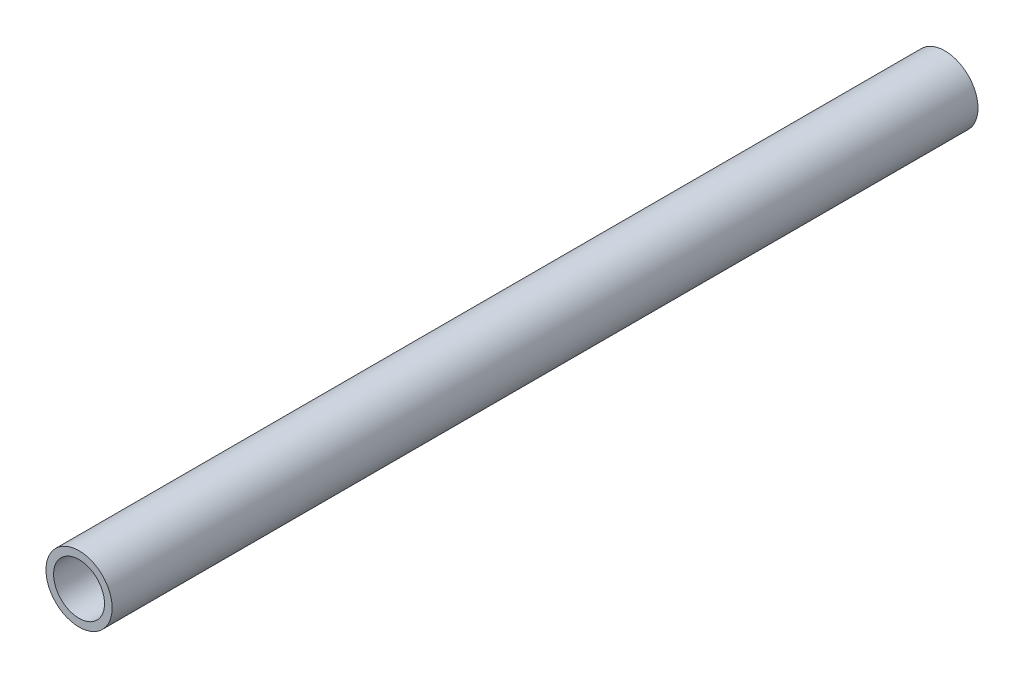
SolidWorks part; units mm, degrees
material "3.0255 (EN-AW 1350A)"
ref_plane "Alzado" through (0, 0, 0) normal (0, 0, 1) x (1, 0, 0)
ref_plane "Planta" through (0, 0, 0) normal (0, 1, 0) x (1, 0, 0)
ref_plane "Vista lateral" through (0, 0, 0) normal (1, 0, 0) x (0, 0, -1)
sketch "Croquis1" plane through (0, 0, 0) normal (0, 0, 1) x (1, 0, 0)
  circle A0 centre (0, 0) radius 5
  circle A1 centre (0, 0) radius 6.5
  dimension "D1" = 13
  dimension "D2" = 1.5
extrude "Saliente-Extruir1" add sketch "Croquis1" along normal mid plane 170
